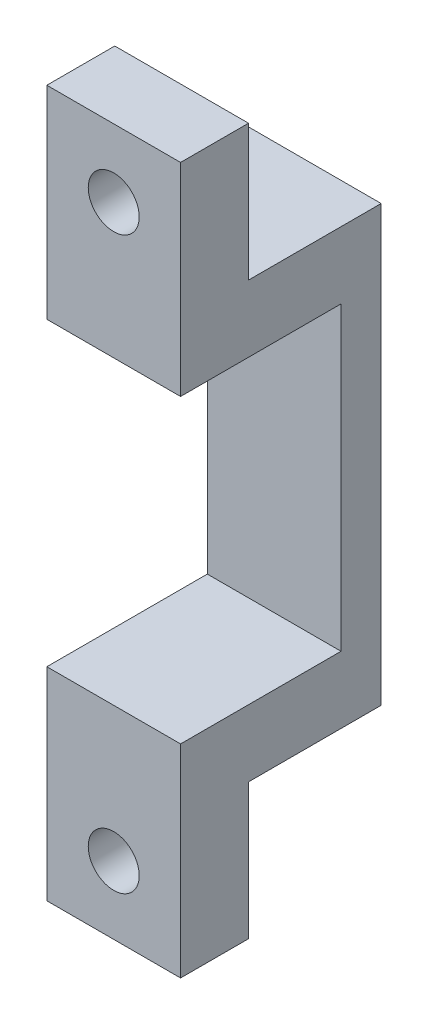
SolidWorks part; units mm, degrees
ref_plane "Front Plane" through (0, 0, 0) normal (0, 0, 1) x (1, 0, 0)
ref_plane "Top Plane" through (0, 0, 0) normal (0, 1, 0) x (1, 0, 0)
ref_plane "Right Plane" through (0, 0, 0) normal (1, 0, 0) x (0, 0, -1)
ref_plane "Plane1" through (0, 0, 0) normal (-1, 0, 0) x (0, -1, 0)
sketch "Sketch1" plane through (0, 0, 0) normal (-1, 0, 0) x (0, -1, 0)
  line L0 (-15.16, 15) -> (-15.16, 0)
  line L1 (-15.16, 0) -> (11.25, 0)
  line L2 (11.25, 0) -> (11.25, 15)
  line L3 (11.25, 15) -> (-15.16, 15)
extrude "Boss-Extrude1" add sketch "Sketch1" against normal blind 10
sketch "Sketch2" plane through (10, 0, 0) normal (1, 0, 0) x (0, 0, -1)
  line L0 (-3, 0) -> (-15, 0)
  line L1 (-15, 0) -> (-15, -11.25)
  line L2 (-15, -11.25) -> (-3, -11.25)
  line L3 (-3, -11.25) -> (-3, 0)
extrude "Cut-Extrude1" cut sketch "Sketch2" against normal through all
sketch "Sketch3" plane through (10, 0, 0) normal (1, 0, 0) x (0, 0, -1)
  line L0 (-9.92, 15.16) -> (-9.92, 5)
  line L1 (-9.92, 5) -> (0, 5)
  line L2 (0, 5) -> (0, 15.16)
  line L3 (0, 15.16) -> (-9.92, 15.16)
extrude "Cut-Extrude2" cut sketch "Sketch3" against normal through all
hole_wizard "M3.5 Clearance Hole1" positions "Sketch5" profile "Sketch4" hole size "M3.5" standard "ANSI Metric"
sketch "Sketch5" plane through (0, 0, 9.92) normal (0, 0, -1) x (-1, 0, 0)
  point P0 (-5, 10.08)
sketch "Sketch4" plane through (5, 10.08, 9.92) normal (1, 0, 0) x (0, 1, 0)
  line L0 (0, 0) -> (0, 5.08)
  line L1 (0, 5.08) -> (1.905, 5.08)
  line L2 (1.905, 5.08) -> (1.905, 0)
  line L5 (1.905, 0) -> (0, 0)
  line L11 (0, -6.35) -> (0, 107.95) construction
  dimension "Thru Hole Dia." = 3.81
  dimension "Thru Hole Depth" = 5.08
hole_wizard "Ø1.2 (1.2) Diameter Hole1" positions "Sketch7" profile "Sketch6" hole size "Ø1.2" standard "ANSI Metric"
sketch "Sketch7" plane through (0, 0, 0) normal (-1, 0, 0) x (0, 0, 1)
  point P0 (9.4882, 2.5)
sketch "Sketch6" plane through (0, 2.5, 9.4882) normal (0, 1, 0) x (0, 0, 1)
  line L0 (0, 0) -> (0, 5.3605)
  line L1 (0, 5.3605) -> (0.6, 5)
  line L2 (0.6, 5) -> (0.6, 0)
  line L5 (0.6, 0) -> (0, 0)
  line L10 (0, 5.3605) -> (-0.6, 5) construction
  line L11 (0, -6.35) -> (0, 107.95) construction
  dimension "Hole Dia." = 1.2
  dimension "Hole Depth" = 5
  dimension "Drill Angle" = 118
ref_plane "Plane2" through (0, -11.25, 0) normal (0, -1, 0) x (-1, 0, 0)
mirror "Mirror1" about plane through (0, -11.25, 0) normal (0, -1, 0) of "Ø1.2 (1.2) Diameter Hole1", "M3.5 Clearance Hole1", "Cut-Extrude2", "Cut-Extrude1", "Boss-Extrude1"
